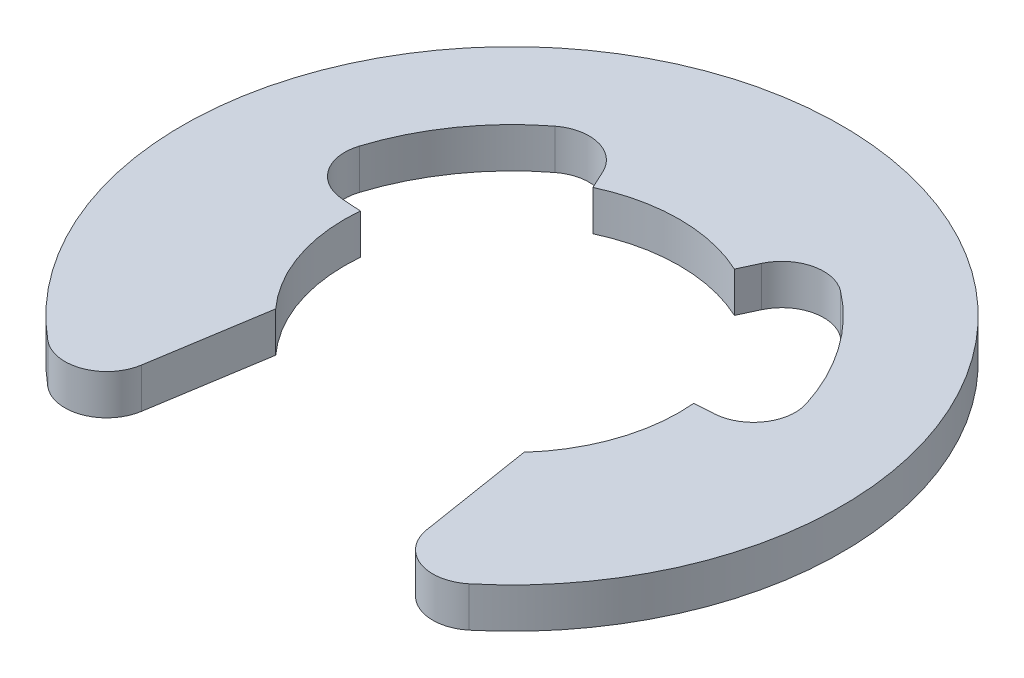
SolidWorks part; units mm, degrees
material "Plain Carbon Steel"
ref_plane "Front Plane" through (0, 0, 0) normal (0, 0, 1) x (1, 0, 0)
ref_plane "Top Plane" through (0, 0, 0) normal (0, 1, 0) x (1, 0, 0)
ref_plane "Right Plane" through (0, 0, 0) normal (1, 0, 0) x (0, 0, -1)
sketch "Sketch1" plane through (0, 0, 0) normal (0, 1, 0) x (1, 0, 0)
  line L0 (2.1131, 4.5315) -> (2.3719, 5.0866)
  line L1 (3.7108, -3.3511) -> (4.2622, -6.8109)
  line L2 (0, 0) -> (5.7341, 4.015) construction
  line L3 (4.98, 0.4468) -> (5.5681, 0.4874)
  line L4 (0, 0) -> (-5.7341, 4.015) construction
  line L5 (-4.98, 0.4468) -> (-5.5681, 0.4874)
  line L6 (-3.7108, -3.3511) -> (-4.2622, -6.8109)
  line L7 (-2.1131, 4.5315) -> (-2.3719, 5.0866)
  line L8 (0, 9.85) -> (0, 5) construction
  line L9 (0, 5) -> (0, 0) construction
  arc A0 (6.2955, -7.5755) -> (-6.2955, -7.5755) centre (0, 0) ccw
  arc A1 (3.7108, -3.3511) -> (4.98, 0.4468) centre (0, 0) ccw
  arc A2 (2.3719, 5.0866) -> (4.2667, 5.5493) centre (3.5048, 4.5584) cw
  arc A3 (2.1131, 4.5315) -> (-2.1131, 4.5315) centre (0, 0) ccw
  arc A4 (6.674, 2.1114) -> (4.2667, 5.5493) centre (0, 0) ccw
  arc A5 (5.5681, 0.4874) -> (6.674, 2.1114) centre (5.4822, 1.7344) ccw
  arc A6 (4.2622, -6.8109) -> (6.2955, -7.5755) centre (5.4966, -6.6142) ccw
  arc A7 (-4.2622, -6.8109) -> (-6.2955, -7.5755) centre (-5.4966, -6.6142) cw
  arc A8 (-5.5681, 0.4874) -> (-6.674, 2.1114) centre (-5.4822, 1.7344) cw
  arc A9 (-6.674, 2.1114) -> (-4.2667, 5.5493) centre (0, 0) cw
  arc A10 (-2.3719, 5.0866) -> (-4.2667, 5.5493) centre (-3.5048, 4.5584) ccw
  arc A11 (-3.7108, -3.3511) -> (-4.98, 0.4468) centre (0, 0) cw
  point P27 (-29.596, 14.4679)
  point P28 (-25.8678, 19.7924)
  dimension "D1" = 10
  dimension "D3" = 1.25
  dimension "D4" = 1.25
  dimension "D6" = 9.85
  dimension "D2" = 30
  dimension "D5" = 3.3511
  dimension "D7" = 7
  dimension "D8" = 110
extrude "Extrude1" add sketch "Sketch1" along normal blind 1.2
